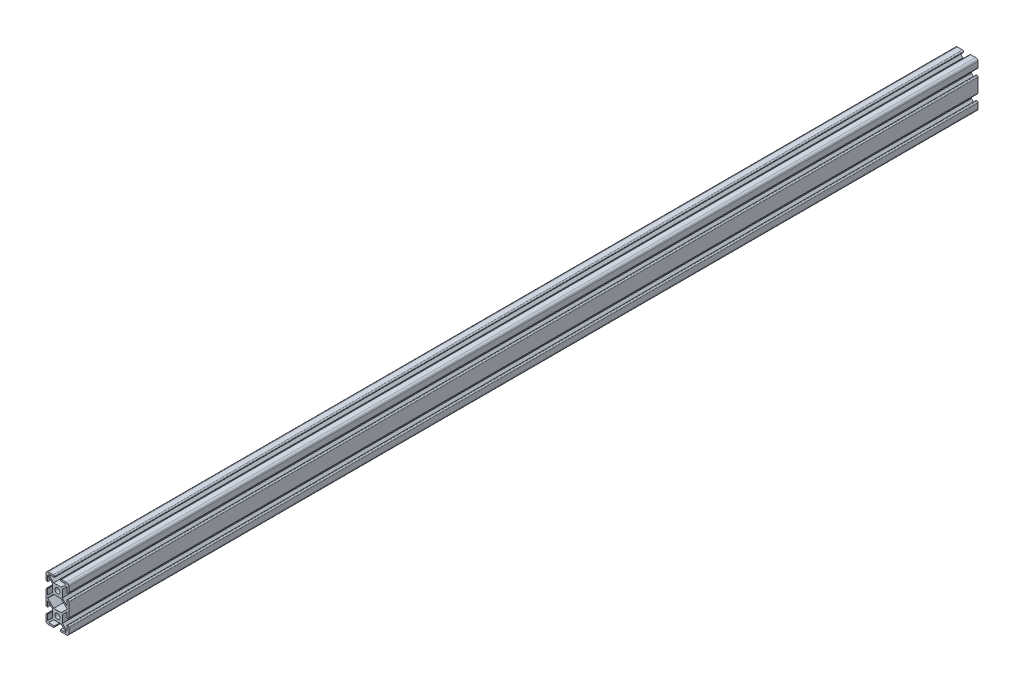
SolidWorks part; units mm, degrees
ref_plane "Alzado" through (0, 0, 0) normal (0, 0, 1) x (1, 0, 0)
ref_plane "Planta" through (0, 0, 0) normal (0, 1, 0) x (1, 0, 0)
ref_plane "Vista lateral" through (0, 0, 0) normal (1, 0, 0) x (0, 0, -1)
sketch "Croquis1" plane through (0, 0, 0) normal (0, 0, 1) x (1, 0, 0)
  line L0 (-15.05, 0) -> (15.05, 0) construction
  line L1 (-12.05, -30.05) -> (-4, -30.05)
  line L2 (-15.05, -27.05) -> (-15.05, -18.55)
  line L3 (-12.05, 30.05) -> (-4, 30.05)
  line L4 (15.05, -27.05) -> (15.05, -18.55)
  line L5 (-15.05, -30.05) -> (15.05, 30.05) construction
  line L6 (-15.05, 30.05) -> (15.05, -30.05) construction
  line L7 (-4, 30.05) -> (-4, 27.75)
  line L8 (-5, 8.05) -> (5, 8.05)
  line L9 (-6.5, 9.55) -> (-6.5, 19.55)
  line L10 (-5, 21.05) -> (5, 21.05)
  line L11 (6.5, 9.55) -> (6.5, 19.55)
  line L12 (-6.5, 8.05) -> (6.5, 21.05) construction
  line L13 (-6.5, 21.05) -> (6.5, 8.05) construction
  line L14 (15.05, 18.55) -> (15.05, 27.05)
  line L15 (-3.35, 11.2) -> (3.35, 11.2) construction
  line L16 (-3.35, 11.2) -> (-3.35, 17.9) construction
  line L17 (-3.35, 17.9) -> (3.35, 17.9) construction
  line L18 (3.35, 11.2) -> (3.35, 17.9) construction
  line L19 (-3.35, 11.2) -> (3.35, 17.9) construction
  line L20 (-3.35, 17.9) -> (3.35, 11.2) construction
  line L21 (-11.7, -27.75) -> (-4, -27.75)
  line L22 (-12.75, -25.8) -> (-12.75, -18.55)
  line L23 (-11.7, 27.75) -> (-4, 27.75)
  line L24 (12.75, -25.8) -> (12.75, -18.55)
  line L25 (-12.75, -27.75) -> (12.75, 27.75) construction
  line L26 (-12.75, 27.75) -> (12.75, -27.75) construction
  line L27 (4, 30.05) -> (4, 27.75)
  line L28 (12.75, 18.55) -> (12.75, 25.8)
  line L31 (-15.05, 18.55) -> (-12.75, 18.55)
  line L32 (-15.05, 10.55) -> (-12.75, 10.55)
  line L33 (15.05, 10.55) -> (12.75, 10.55)
  line L34 (15.05, 18.55) -> (12.75, 18.55)
  line L36 (-5, 21.05) -> (-11.7, 27.75)
  line L37 (-6.5, 21.05) -> (-12.75, 27.75) construction
  line L39 (-6.5, 19.55) -> (-12.75, 25.8)
  line L40 (6.5, 19.55) -> (12.75, 25.8)
  line L41 (5, 21.05) -> (11.7, 27.75)
  line L42 (6.5, -19.55) -> (12.75, -25.8)
  line L43 (5, -21.05) -> (11.7, -27.75)
  line L44 (-15.05, -30.05) -> (-4, -30.05)
  line L45 (-15.05, 30.05) -> (-4, 30.05)
  line L46 (-6.5, -19.55) -> (-12.75, -25.8)
  line L47 (-5, -21.05) -> (-11.7, -27.75)
  line L48 (4, -30.05) -> (4, -27.75)
  line L49 (-4, -30.05) -> (-4, -27.75)
  line L50 (-15.05, -10.55) -> (-12.75, -10.55)
  line L51 (-15.05, -18.55) -> (-12.75, -18.55)
  line L52 (15.05, -18.55) -> (12.75, -18.55)
  line L53 (15.05, -10.55) -> (12.75, -10.55)
  line L54 (-3.35, -11.2) -> (-3.35, -17.9) construction
  line L55 (-3.35, -17.9) -> (3.35, -17.9) construction
  line L56 (3.35, -11.2) -> (3.35, -17.9) construction
  line L57 (-3.35, -11.2) -> (3.35, -11.2) construction
  line L58 (-5, -8.05) -> (5, -8.05)
  line L59 (6.5, -9.55) -> (6.5, -19.55)
  line L60 (-6.5, -9.55) -> (-6.5, -19.55)
  line L61 (-5, -21.05) -> (5, -21.05)
  line L62 (4, -30.05) -> (12.05, -30.05)
  line L63 (6.5, -9.55) -> (12.75, -3.3)
  line L64 (5, -8.05) -> (11.7, -1.35)
  line L65 (-5, -8.05) -> (-11.7, -1.35)
  line L66 (-6.5, -9.55) -> (-12.75, -3.3)
  line L67 (-11.7, -1.35) -> (-12.75, -0.3)
  line L68 (11.7, -1.35) -> (12.75, -0.3)
  line L69 (-12.75, -0.3) -> (-12.75, 0.3)
  line L70 (12.75, -0.3) -> (12.75, 0.3)
  line L71 (6.5, 9.55) -> (12.75, 3.3)
  line L72 (5, 8.05) -> (11.7, 1.35)
  line L73 (-6.5, 9.55) -> (-12.75, 3.3)
  line L74 (-5, 8.05) -> (-11.7, 1.35)
  line L75 (-11.7, 1.35) -> (-12.75, 0.3)
  line L76 (11.7, 1.35) -> (12.75, 0.3)
  line L77 (-12.75, 3.3) -> (-12.75, 10.55)
  line L78 (12.75, 3.3) -> (12.75, 10.55)
  line L79 (15.05, -10.55) -> (15.05, 10.55)
  line L80 (12.75, -10.55) -> (12.75, -3.3)
  line L81 (-15.05, -10.55) -> (-15.05, 10.55)
  line L82 (-12.75, -10.55) -> (-12.75, -3.3)
  line L83 (4, -30.05) -> (15.05, -30.05)
  line L84 (4, -27.75) -> (11.7, -27.75)
  line L85 (4, 30.05) -> (12.05, 30.05)
  line L86 (4, 30.05) -> (15.05, 30.05)
  line L87 (4, 27.75) -> (11.7, 27.75)
  line L88 (-12.75, 18.55) -> (-12.75, 25.8)
  line L89 (-15.05, 18.55) -> (-15.05, 27.05)
  arc A0 (-12.05, -30.05) -> (-15.05, -27.05) centre (-12.05, -27.05) cw
  arc A1 (12.05, -30.05) -> (15.05, -27.05) centre (12.05, -27.05) ccw
  arc A2 (12.05, 30.05) -> (15.05, 27.05) centre (12.05, 27.05) cw
  arc A3 (-15.05, 27.05) -> (-12.05, 30.05) centre (-12.05, 27.05) cw
  circle A4 centre (0, 14.55) radius 3.35
  circle A5 centre (0, -14.55) radius 3.35
  point P0 (0, 0)
  point P8 (0, 14.55)
  point P9 (0, 14.55)
  point P20 (0, 0)
  point P55 (0, 11.2)
  point P72 (0, -11.2)
  dimension "D10" = 3
  dimension "D1" = 60.1
  dimension "D2" = 30.1
  dimension "D3" = 13
  dimension "D4" = 13
  dimension "D5" = 22
  dimension "D6" = 25.5
  dimension "D7" = 6.7
  dimension "D8" = 6.7
  dimension "D9" = 55.5
  dimension "D12" = 1.5
  dimension "D13" = 135
  dimension "D14" = 1.5
  dimension "D15" = 135
extrude "Saliente-Extruir1" add sketch "Croquis1" along normal blind 1200 contours L89 L31 L88 L39 L9 L73 L77 L32 L81 L50 L82 L66 L60 L46 L22 L51 L2 L1 L49 L21 L47 L61 L43 L84 L48 L62 L4 L52 L24 L42 L59 L63 L80 L53 L79 L33 L78 L71 L11 L40 L28 L34 L14 L85 L27 L87 L41 L10 L36 L23 L7
fillet "Redondeo1" radius 1.5 12 edges at (-4, -30.05, 600) (15.05, -10.55, 600) (15.05, 18.55, 600) (4, 30.05, 600) (-4, 30.05, 600) (15.05, 10.55, 600) (15.05, -18.55, 600) (4, -30.05, 600) (-15.05, -18.55, 600) (-15.05, -10.55, 600) (-15.05, 10.55, 600) (-15.05, 18.55, 600)
